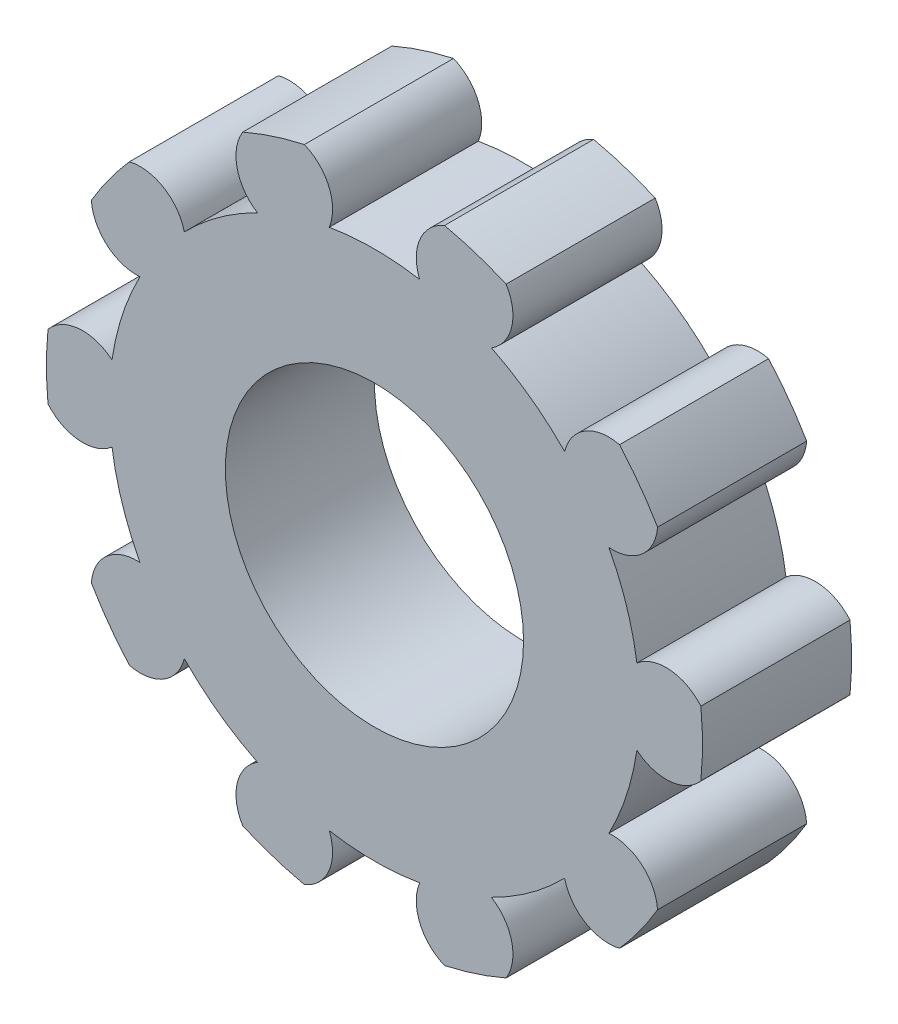
SolidWorks part; units mm, degrees
ref_plane "Front Plane" through (0, 0, 0) normal (0, 0, 1) x (1, 0, 0)
ref_plane "Top Plane" through (0, 0, 0) normal (0, 1, 0) x (1, 0, 0)
ref_plane "Right Plane" through (0, 0, 0) normal (1, 0, 0) x (0, 0, -1)
sketch "Sketch1" plane through (0, 0, 0) normal (0, 0, 1) x (1, 0, 0)
  circle A0 centre (0, 0) radius 6
  circle A1 centre (0, 0) radius 13.2
extrude "Boss-Extrude1" add sketch "Sketch1" along normal blind 6
sketch "Sketch2" plane through (0, 0, 6) normal (0, 0, 1) x (1, 0, 0)
  line L0 (0, 0) -> (0, 15.2) construction
  line L1 (-1.8199, 15.2) -> (0, 0) construction
  line L2 (1.8199, 15.2) -> (0, 0) construction
  arc A0 (-1.8199, 12) -> (1.8199, 12) centre (0, 0) cw
  arc A1 (-2.8199, 12.8953) -> (2.8199, 12.8953) centre (0, 0) cw
  arc A2 (-1.8199, 10.512) -> (1.8199, 10.512) centre (0, 0) cw
  arc A3 (-2.8199, 12.8953) -> (-1.8199, 10.512) centre (-3.5115, 11.2036) cw
  arc A4 (2.8199, 12.8953) -> (1.8199, 10.512) centre (3.5115, 11.2036) ccw
extrude "Cut-Extrude1" cut sketch "Sketch2" against normal through all contours A1 A4 A2 A3
pattern_circular "CirPattern1" count 10 over 360 about axis through (0, 0, 0) along (0, 0, 1) of "Cut-Extrude1"
